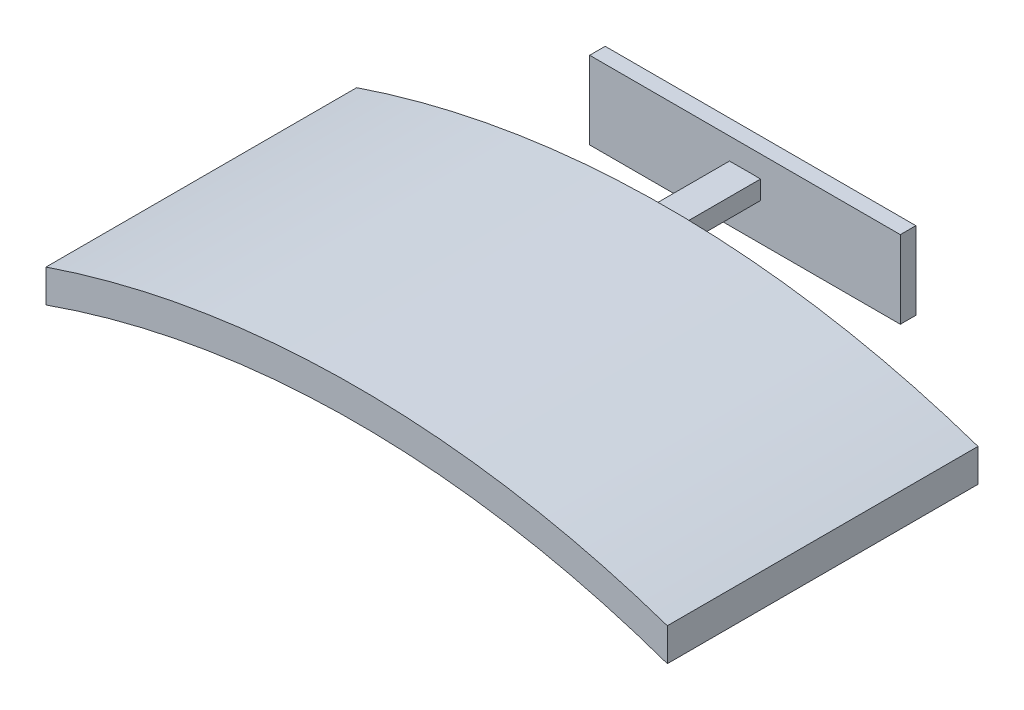
SolidWorks part; units mm, degrees
ref_plane "Front Plane" through (0, 0, 0) normal (0, 0, 1) x (1, 0, 0)
ref_plane "Top Plane" through (0, 0, 0) normal (0, 1, 0) x (1, 0, 0)
ref_plane "Right Plane" through (0, 0, 0) normal (1, 0, 0) x (0, 0, -1)
sketch "Sketch1" plane through (0, 0, 0) normal (0, 0, 1) x (1, 0, 0)
  line L0 (0, 0) -> (0, 21.1706)
  line L1 (400, 0) -> (400, 21.1706)
  arc A0 (0, 0) -> (400, 0) centre (200, -565.6854) cw
  arc A1 (0, 21.1706) -> (400, 21.1706) centre (200, -565.6854) cw
  arc A2 (-6.6667, 18.8562) -> (406.6667, 18.8562) centre (200, -565.6854) cw construction
  dimension "D1" = 600
  dimension "D3" = 400
  dimension "D2" = 20
extrude "Boss-Extrude1" add sketch "Sketch1" along normal blind 200
sketch "Sketch3" plane through (0, 0, 200) normal (0, 0, 1) x (1, 0, 0)
  line L0 (2, 1.7624) -> (2, 0.7031)
  line L1 (0, 21.1706) -> (0, 0) construction
  line L2 (400, 0) -> (400, 21.1706)
  line L3 (0, 21.1706) -> (0, 0)
  line L6 (200, 34.3146) -> (200, 30.6157) construction
  line L7 (398, 1.7624) -> (398, 0.7031)
  arc A0 (398, 1.7624) -> (2, 1.7624) centre (200, -565.6854) ccw
  arc A1 (400.3333, 0.9428) -> (-0.3333, 0.9428) centre (200, -565.6854) ccw construction
  arc A2 (400, 0) -> (0, 0) centre (200, -565.6854) ccw
  arc A3 (400, 21.1706) -> (0, 21.1706) centre (200, -565.6854) ccw
  arc A4 (398, 0.7031) -> (2, 0.7031) centre (200, -565.6854) ccw
  arc A6 (400, 0) -> (0, 0) centre (200, -565.6854) ccw construction
  dimension "D3" = 2
  dimension "D1" = 0
  dimension "D2" = 1
extrude "Cut-Extrude1" cut sketch "Sketch3" against normal blind 196 from offset 2 offset against normal yes
sketch "Sketch5" plane through (0, 0, 0) normal (0, 0, -1) x (-1, 0, 0)
  line L0 (-200, 34.3146) -> (-200, 95.7081) construction
  line L1 (-210, 50.2334) -> (-210, 38.2318)
  line L5 (-190, 50.2334) -> (-190, 38.2318)
  arc A0 (-190, 50.2334) -> (-210, 50.2334) centre (-200, -565.6854) ccw
  arc A1 (-190, 38.2318) -> (-210, 38.2318) centre (-200, -565.6854) ccw
  dimension "D4" = 10
extrude "Boss-Extrude3" add sketch "Sketch5" along normal blind 50
sketch "Sketch6" plane through (0, 0, -50) normal (0, 0, -1) x (-1, 0, 0)
  line L1 (-300, 64.2326) -> (-100, 64.2326)
  line L2 (-300, 64.2326) -> (-300, 14.2326)
  line L7 (-300, 14.2326) -> (-100, 14.2326)
  line L8 (-100, 64.2326) -> (-100, 14.2326)
  line L10 (-190, 50.2334) -> (-210, 38.2318) construction
  line L11 (-210, 50.2334) -> (-190, 38.2318) construction
  point P2 (-200, 64.2326)
  point P7 (-200, 44.2326)
  point P8 (-177.0492, 44.2326)
  dimension "D3" = 20
  dimension "D1" = 200
  dimension "D2" = 50
extrude "Boss-Extrude4" add sketch "Sketch6" along normal blind 10
